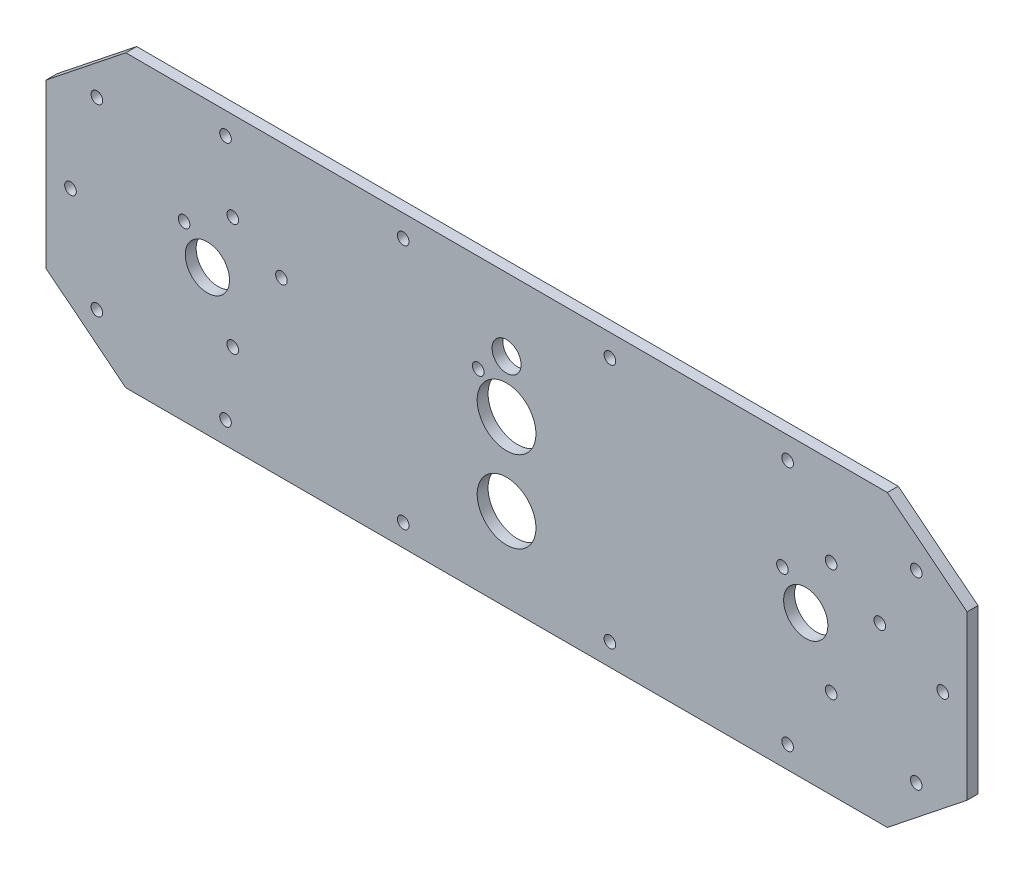
SolidWorks part; units mm, degrees
ref_plane "Alzado" through (0, 0, 0) normal (0, 0, 1) x (1, 0, 0)
ref_plane "Planta" through (0, 0, 0) normal (0, 1, 0) x (1, 0, 0)
ref_plane "Vista lateral" through (0, 0, 0) normal (1, 0, 0) x (0, 0, -1)
sketch "Croquis1" plane through (0, 0, 0) normal (0, 0, 1) x (1, 0, 0)
  line L0 (-127, 22.5) -> (-105, 40)
  line L1 (127, -40) -> (-127, -40) construction
  line L2 (127, -40) -> (127, 40) construction
  line L3 (127, 40) -> (-127, 40) construction
  line L4 (-127, -40) -> (-127, 40) construction
  line L5 (127, -40) -> (-127, 40) construction
  line L6 (127, 40) -> (-127, -40) construction
  line L7 (-105, 40) -> (105, 40)
  line L8 (105, 40) -> (127, 22.5)
  line L9 (127, 22.5) -> (127, -22.5)
  line L10 (127, -22.5) -> (105, -40)
  line L11 (105, -40) -> (-105, -40)
  line L12 (-105, -40) -> (-127, -22.5)
  line L13 (-127, -22.5) -> (-127, 22.5)
  line L14 (0, -40) -> (0, 40) construction
  line L15 (0, 33.9) -> (-28.5, 33.9) construction
  line L16 (-28.5, 33.9) -> (-77.5, 33.9) construction
  line L17 (0, 33.9) -> (28.5, 33.9) construction
  line L18 (28.5, 33.9) -> (77.5, 33.9) construction
  line L19 (0, -33.9) -> (-28.5, -33.9) construction
  line L20 (-28.5, -33.9) -> (-77.5, -33.9) construction
  line L21 (0, -33.9) -> (28.5, -33.9) construction
  line L22 (28.5, -33.9) -> (77.5, -33.9) construction
  line L23 (-127, 0) -> (-120.25, 0) construction
  line L24 (127, 0) -> (120.25, 0) construction
  line L25 (0, 0) -> (-82.5, 0) construction
  line L26 (-112.98, -25.35) -> (112.98, -25.35) construction
  line L27 (-112.98, -25.35) -> (-112.98, 25.35) construction
  line L28 (-112.98, 25.35) -> (112.98, 25.35) construction
  line L29 (112.98, -25.35) -> (112.98, 25.35) construction
  line L30 (-112.98, -25.35) -> (112.98, 25.35) construction
  line L31 (-112.98, 25.35) -> (112.98, -25.35) construction
  line L32 (0, 0) -> (82.5, 0) construction
  line L33 (-88.9234, 7.75) -> (-75.5, 0) construction
  line L34 (-75.5, 0) -> (-62.0766, 7.75) construction
  line L35 (76.0766, 7.75) -> (89.5, 0) construction
  line L36 (89.5, 0) -> (102.9234, 7.75) construction
  line L37 (82.5, 0) -> (89.5, 0) construction
  circle A0 centre (0, 20) radius 4
  circle A1 centre (112.98, 25.35) radius 1.6
  circle A2 centre (120.25, 0) radius 1.6
  circle A3 centre (112.98, -25.35) radius 1.6
  circle A4 centre (77.5, -33.9) radius 1.6
  circle A5 centre (28.5, -33.9) radius 1.6
  circle A6 centre (-28.5, -33.9) radius 1.6
  circle A7 centre (-77.5, -33.9) radius 1.6
  circle A8 centre (-112.98, -25.35) radius 1.6
  circle A9 centre (-120.25, 0) radius 1.6
  circle A10 centre (-112.98, 25.35) radius 1.6
  circle A11 centre (-77.5, 33.9) radius 1.6
  circle A12 centre (-28.5, 33.9) radius 1.6
  circle A13 centre (28.5, 33.9) radius 1.6
  circle A14 centre (77.5, 33.9) radius 1.6
  circle A15 centre (-82.5, 0) radius 6.1
  circle A16 centre (82.5, 0) radius 6.1
  circle A17 centre (0, 5.55) radius 8.1
  circle A18 centre (0, -16.95) radius 8.1
  circle A19 centre (-7.8, 13.1) radius 1.6
  circle A20 centre (-75.5, 0) radius 15.5 construction
  circle A21 centre (-88.9234, 7.75) radius 1.6
  circle A22 centre (-62.0766, 7.75) radius 1.6
  circle A23 centre (-75.5, 15.5) radius 1.6
  circle A24 centre (-75.5, -15.5) radius 1.6
  circle A25 centre (89.5, 0) radius 15.5 construction
  circle A26 centre (89.5, 15.5) radius 1.6
  circle A27 centre (89.5, -15.5) radius 1.6
  circle A28 centre (76.0766, 7.75) radius 1.6
  circle A29 centre (102.9234, 7.75) radius 1.6
  point P0 (0, 0)
  point P34 (0, 0)
  dimension "D10" = 8
  dimension "D19" = 3.2
  dimension "D21" = 12.2
  dimension "D23" = 16.2
  dimension "D27" = 3.2
  dimension "D28" = 31
  dimension "D30" = 120
  dimension "D31" = 31
  dimension "D34" = 3.2
  dimension "D1" = 254
  dimension "D2" = 80
  dimension "D3" = 22
  dimension "D4" = 22
  dimension "D5" = 22
  dimension "D6" = 22
  dimension "D7" = 17.5
  dimension "D8" = 17.5
  dimension "D9" = 17.5
  dimension "D11" = 20
  dimension "D12" = 57
  dimension "D13" = 6.1
  dimension "D14" = 6.1
  dimension "D15" = 49
  dimension "D16" = 6.75
  dimension "D17" = 7.98
  dimension "D18" = 2.85
  dimension "D20" = 165
  dimension "D22" = 22.5
  dimension "D24" = 14.45
  dimension "D25" = 7.8
  dimension "D26" = 7.55
  dimension "D29" = 7
  dimension "D32" = 120
  dimension "D33" = 7
extrude "Saliente-Extruir1" add sketch "Croquis1" along normal blind 3
